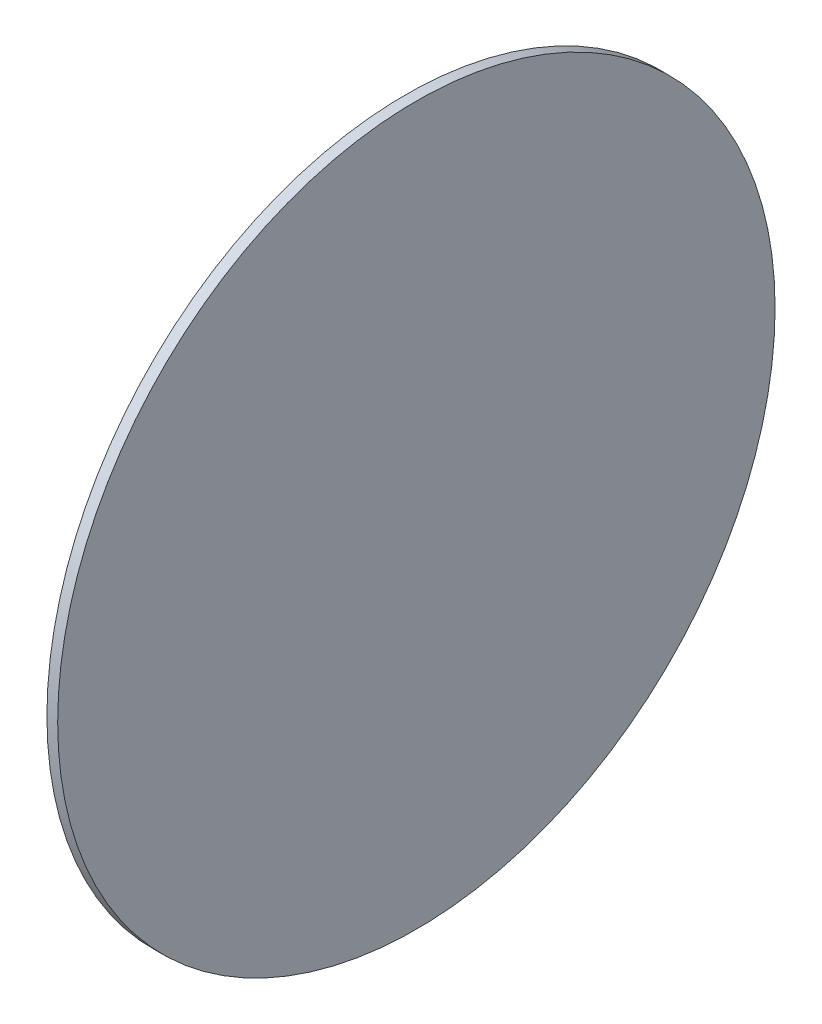
SolidWorks part; units mm, degrees
ref_plane "Front Plane" through (0, 0, 0) normal (0, 0, 1) x (1, 0, 0)
ref_plane "Top Plane" through (0, 0, 0) normal (0, 1, 0) x (1, 0, 0)
ref_plane "Right Plane" through (0, 0, 0) normal (1, 0, 0) x (0, 0, -1)
sketch "Sketch1" plane through (0, 0, 0) normal (1, 0, 0) x (0, 0, -1)
  circle A0 centre (0, 0) radius 100
  dimension "D1" = 200
extrude "Boss-Extrude1" add sketch "Sketch1" along normal blind 3
